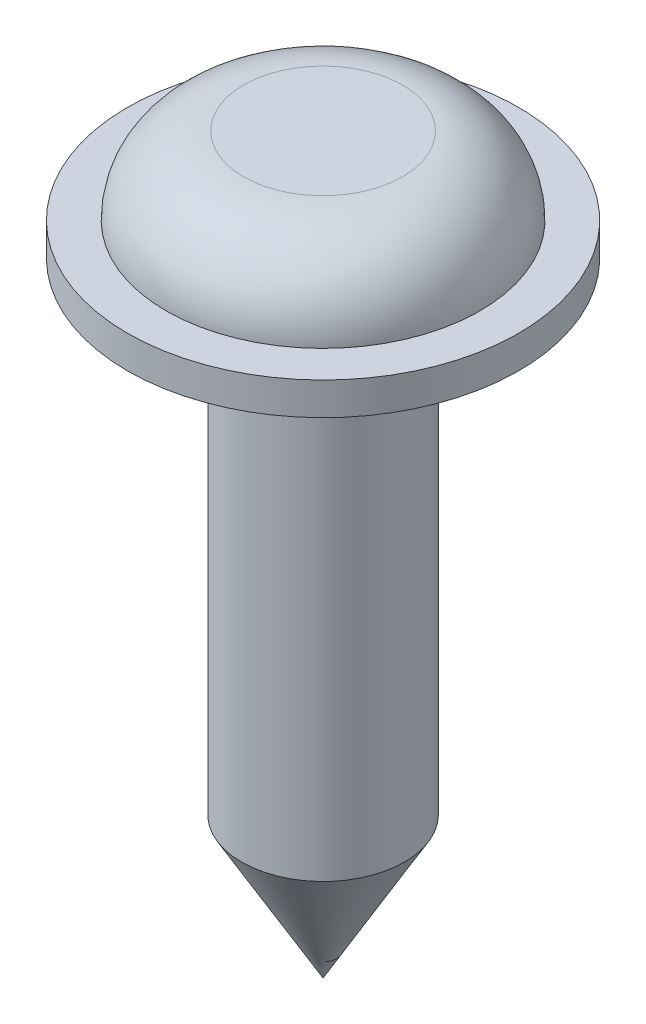
SolidWorks part; units mm, degrees
ref_plane "Plan de face" through (0, 0, 0) normal (0, 0, 1) x (1, 0, 0)
ref_plane "Plan de dessus" through (0, 0, 0) normal (0, 1, 0) x (1, 0, 0)
ref_plane "Plan de droite" through (0, 0, 0) normal (1, 0, 0) x (0, 0, -1)
sketch "Esquisse1" plane through (0, 0, 0) normal (0, 0, 1) x (1, 0, 0)
  line L0 (0, 0) -> (0, 9) construction
  line L1 (0, 0) -> (1, 1.7321)
  line L2 (1, 1.7321) -> (1, 7.65)
  line L3 (1, 7.65) -> (2.4, 7.65)
  line L4 (2.4, 7.65) -> (2.4, 8.05)
  line L5 (2.4, 8.05) -> (1.925, 8.05)
  line L6 (0, 9) -> (0.975, 9)
  line L7 (0, 9) -> (0, 0)
  arc A0 (1.925, 8.05) -> (0.975, 9) centre (0.975, 8.05) ccw
  dimension "D1" = 9
  dimension "D2" = 1
  dimension "D3" = 30
  dimension "D4" = 7.65
  dimension "D5" = 0.4
  dimension "D6" = 1.925
  dimension "D7" = 2.4
  dimension "D8" = 0.95
revolve "Révolution1" add sketch "Esquisse1" angle 360 about L7
